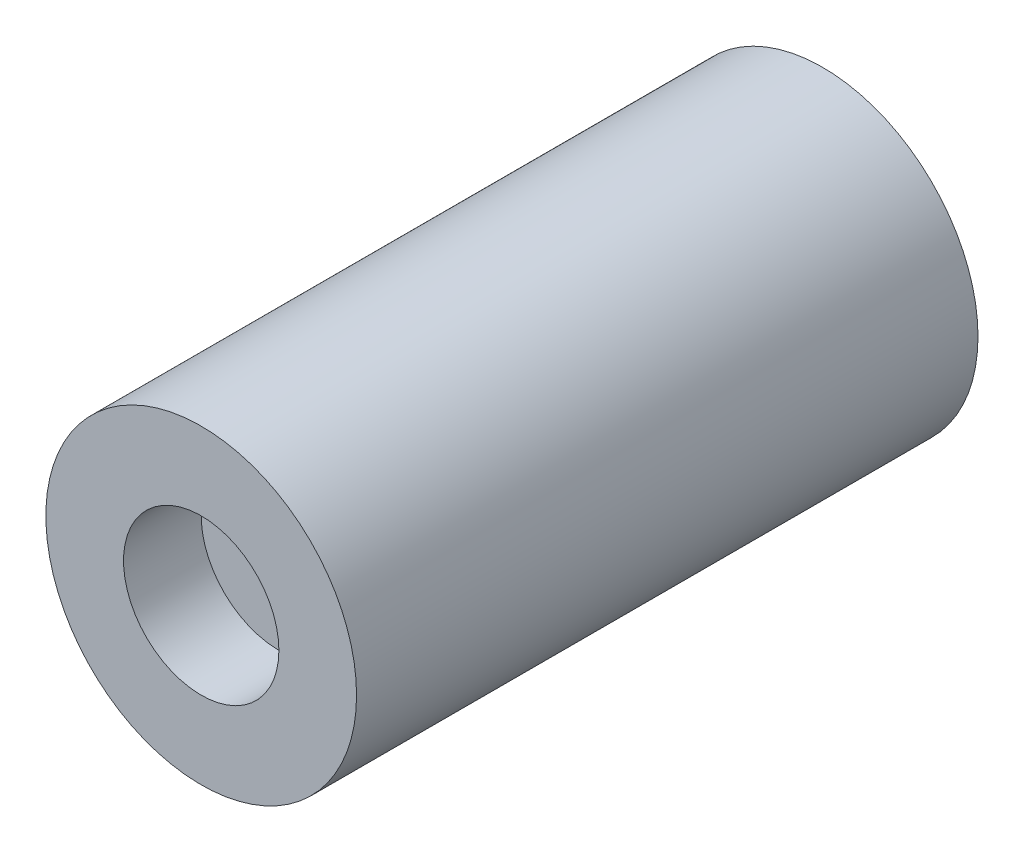
SolidWorks part; units mm, degrees
ref_plane "Plan de face" through (0, 0, 0) normal (0, 0, 1) x (1, 0, 0)
ref_plane "Plan de dessus" through (0, 0, 0) normal (0, 1, 0) x (1, 0, 0)
ref_plane "Plan de droite" through (0, 0, 0) normal (1, 0, 0) x (0, 0, -1)
sketch "Esquisse1" plane through (0, 0, 0) normal (0, 0, 1) x (1, 0, 0)
  circle A0 centre (0, 0) radius 10
  dimension "D1" = 20
extrude "Boss.-Extru.1" add sketch "Esquisse1" along normal blind 40
sketch "Esquisse2" plane through (0, 0, 40) normal (0, 0, 1) x (1, 0, 0)
  circle A0 centre (0, 0) radius 5
  dimension "D1" = 10
extrude "Enlèv. mat.-Extru.1" cut sketch "Esquisse2" against normal blind 5
